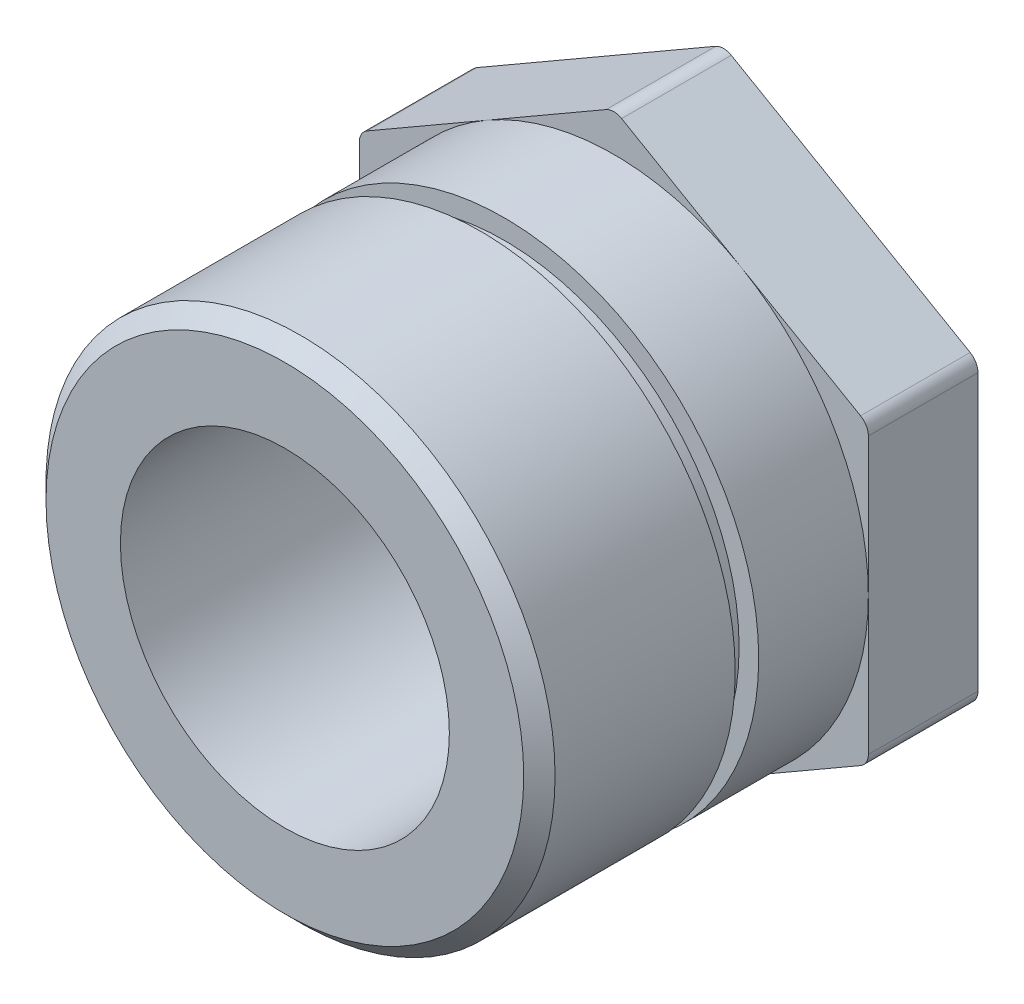
SolidWorks part; units mm, degrees
ref_plane "Front Plane" through (0, 0, 0) normal (0, 0, 1) x (1, 0, 0)
ref_plane "Top Plane" through (0, 0, 0) normal (0, 1, 0) x (1, 0, 0)
ref_plane "Right Plane" through (0, 0, 0) normal (1, 0, 0) x (0, 0, -1)
sketch "Sketch1" plane through (0, 0, 0) normal (0, 0, 1) x (1, 0, 0)
  circle A0 centre (0, 0) radius 32.5
  dimension "D1" = 65
extrude "Boss-Extrude1" add sketch "Sketch1" along normal blind 42
cosmetic thread "Cosmetic Thread1" parameters "D1"=25, "D2"=59.61
sketch "Sketch2" plane through (0, 0, 42) normal (0, 0, 1) x (1, 0, 0)
  circle A0 centre (0, 0) radius 30
  circle A1 centre (0, 0) radius 32.5
  circle A2 centre (0, 0) radius 32.5
  dimension "D2" = 60
  dimension "D1" = 0
extrude "Cut-Extrude1" cut sketch "Sketch2" along normal blind 3 from offset 28 offset against normal yes
sketch "Sketch3" plane through (0, 0, 0) normal (0, 0, -1) x (-1, 0, 0)
  line L1 (32.5, -18.7639) -> (32.5, 18.7639)
  line L2 (32.5, 18.7639) -> (0, 37.5278)
  line L3 (0, 37.5278) -> (-32.5, 18.7639)
  line L4 (-32.5, 18.7639) -> (-32.5, -18.7639)
  line L5 (-32.5, -18.7639) -> (0, -37.5278)
  line L6 (0, -37.5278) -> (32.5, -18.7639)
  circle A0 centre (0, 0) radius 32.5 construction
  circle A1 centre (0, 0) radius 32.5 construction
extrude "Boss-Extrude3" add sketch "Sketch3" along normal blind 14
fillet "Fillet1" radius 2 6 edges at (0, -37.5278, -7) (32.5, -18.7639, -7) (32.5, 18.7639, -7) (-32.5, 18.7639, -7) (-32.5, -18.7639, -7) (0, 37.5278, -7)
chamfer "Chamfer1" distance 2 angle 45 1 edges at (32.5, 0, 42)
sketch "Sketch4" plane through (0, 0, 42) normal (0, 0, 1) x (1, 0, 0)
  circle A0 centre (0, 0) radius 21
  dimension "D1" = 42
extrude "Cut-Extrude4" cut sketch "Sketch4" against normal through all
